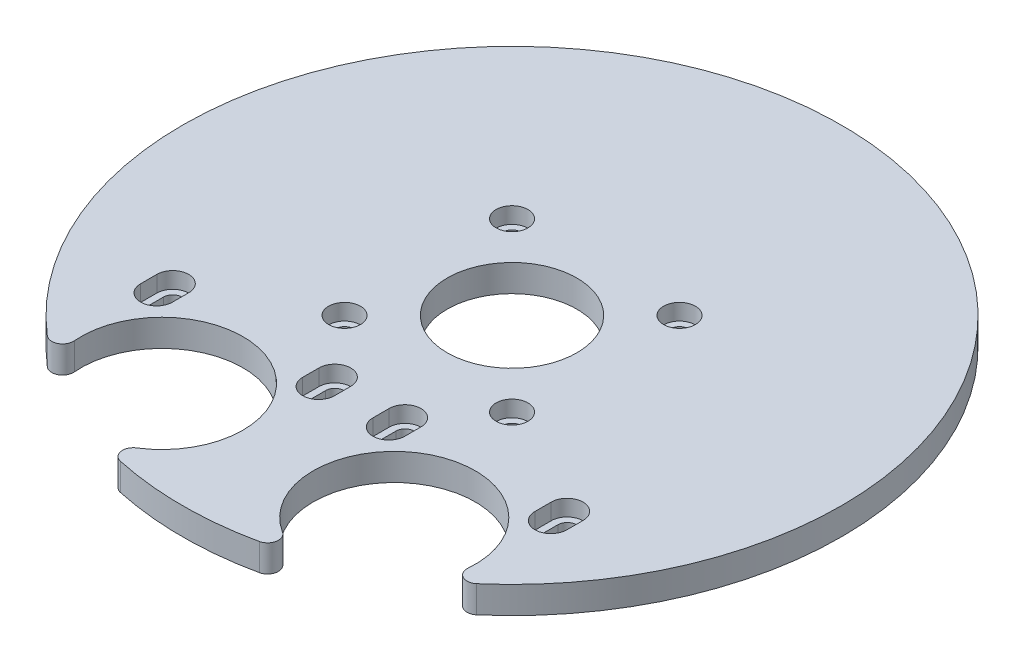
SolidWorks part; units mm, degrees
material "PLA"
ref_plane "Alzado" through (0, 0, 0) normal (0, 0, 1) x (1, 0, 0)
ref_plane "Planta" through (0, 0, 0) normal (0, 1, 0) x (1, 0, 0)
ref_plane "Vista lateral" through (0, 0, 0) normal (1, 0, 0) x (0, 0, -1)
sketch "Croquis1" plane through (0, 0, 0) normal (0, 1, 0) x (1, 0, 0)
  line L0 (0, 12) -> (0, -57.1022) construction
  arc A0 (-12.8483, -59.6315) -> (12.8483, -59.6315) centre (0, 0) ccw
  circle A1 centre (0, 0) radius 12
  arc A2 (-13.4944, -55.9851) -> (-36.4445, -44.5896) centre (-21.5, -43.3) ccw
  arc A4 (13.4944, -55.9851) -> (36.4445, -44.5896) centre (21.5, -43.3) cw
  arc A5 (39.74, -46.2788) -> (-39.74, -46.2788) centre (0, 0) ccw
  arc A6 (36.4445, -44.5896) -> (39.74, -46.2788) centre (38.4371, -44.7615) ccw
  arc A7 (13.4944, -55.9851) -> (12.8483, -59.6315) centre (12.427, -57.6764) cw
  arc A8 (-12.8483, -59.6315) -> (-13.4944, -55.9851) centre (-12.427, -57.6764) cw
  arc A9 (-39.74, -46.2788) -> (-36.4445, -44.5896) centre (-38.4371, -44.7615) ccw
  point P13 (34.9085, -50.0239)
  dimension "D3" = 30
  dimension "D4" = 24
  dimension "D5" = 122
  dimension "D6" = 2
  dimension "D1" = 21.5
  dimension "D2" = 43.3
extrude "Saliente-Extruir1" add sketch "Croquis1" along normal blind 5
sketch "Croquis2" plane through (0, 5, 0) normal (0, 1, 0) x (1, 0, 0)
  line L0 (-36.5, -26.3) -> (-36.5, -29.3) construction
  line L1 (15.5, -15.5) -> (-15.5, -15.5) construction
  line L2 (15.5, -15.5) -> (15.5, 15.5) construction
  line L3 (15.5, 15.5) -> (-15.5, 15.5) construction
  line L4 (-15.5, -15.5) -> (-15.5, 15.5) construction
  line L5 (15.5, -15.5) -> (-15.5, 15.5) construction
  line L6 (15.5, 15.5) -> (-15.5, -15.5) construction
  line L7 (-34.8, -26.3) -> (-34.8, -29.3)
  line L8 (-38.2, -26.3) -> (-38.2, -29.3)
  line L9 (-6.5, -26.3) -> (-6.5, -29.3) construction
  line L10 (-4.8, -26.3) -> (-4.8, -29.3)
  line L11 (-8.2, -26.3) -> (-8.2, -29.3)
  line L12 (0, 12) -> (0, -60.2233) construction
  line L13 (6.5, -26.3) -> (6.5, -29.3) construction
  line L14 (4.8, -26.3) -> (4.8, -29.3)
  line L15 (8.2, -26.3) -> (8.2, -29.3)
  line L16 (36.5, -26.3) -> (36.5, -29.3) construction
  line L17 (34.8, -26.3) -> (34.8, -29.3)
  line L18 (38.2, -26.3) -> (38.2, -29.3)
  circle A0 centre (-15.5, 15.5) radius 1.7
  circle A1 centre (-15.5, -15.5) radius 1.7
  circle A2 centre (15.5, -15.5) radius 1.7
  circle A3 centre (15.5, 15.5) radius 1.7
  arc A4 (-34.8, -26.3) -> (-38.2, -26.3) centre (-36.5, -26.3) ccw
  arc A5 (-38.2, -29.3) -> (-34.8, -29.3) centre (-36.5, -29.3) ccw
  arc A6 (-4.8, -26.3) -> (-8.2, -26.3) centre (-6.5, -26.3) ccw
  arc A7 (-8.2, -29.3) -> (-4.8, -29.3) centre (-6.5, -29.3) ccw
  arc A8 (-13.4944, -55.9851) -> (-36.4445, -44.5896) centre (-21.5, -43.3) ccw construction
  circle A9 centre (0, 0) radius 12 construction
  arc A10 (4.8, -26.3) -> (8.2, -26.3) centre (6.5, -26.3) cw
  arc A11 (8.2, -29.3) -> (4.8, -29.3) centre (6.5, -29.3) cw
  arc A12 (34.8, -26.3) -> (38.2, -26.3) centre (36.5, -26.3) cw
  arc A13 (38.2, -29.3) -> (34.8, -29.3) centre (36.5, -29.3) cw
  point P0 (0, 0)
  point P12 (-36.5, -27.8)
  point P17 (-6.5, -27.8)
  point P35 (6.5, -27.8)
  point P42 (36.5, -27.8)
  dimension "D2" = 3.4
  dimension "D5" = 15
  dimension "D7" = 1.7
  dimension "D1" = 31
  dimension "D3" = 14
  dimension "D4" = 15
  dimension "D6" = 3
extrude "Cortar-Extruir1" cut sketch "Croquis2" against normal blind 5
sketch "Croquis3" plane through (0, 5, 0) normal (0, 1, 0) x (1, 0, 0)
  line L0 (-36.5, -26.3) -> (-36.5, -29.3) construction
  line L1 (-33.55, -26.3) -> (-33.55, -29.3)
  line L2 (-39.45, -26.3) -> (-39.45, -29.3)
  line L3 (-6.5, -26.3) -> (-6.5, -29.3) construction
  line L4 (-3.55, -26.3) -> (-3.55, -29.3)
  line L5 (-9.45, -26.3) -> (-9.45, -29.3)
  line L6 (6.5, -26.3) -> (6.5, -29.3) construction
  line L7 (9.45, -26.3) -> (9.45, -29.3)
  line L8 (3.55, -26.3) -> (3.55, -29.3)
  line L9 (36.5, -26.3) -> (36.5, -29.3) construction
  line L10 (39.45, -26.3) -> (39.45, -29.3)
  line L11 (33.55, -26.3) -> (33.55, -29.3)
  circle A0 centre (-15.5, 15.5) radius 2.95
  circle A1 centre (15.5, 15.5) radius 2.95
  circle A2 centre (15.5, -15.5) radius 2.95
  circle A3 centre (-15.5, -15.5) radius 2.95
  arc A4 (-33.55, -26.3) -> (-39.45, -26.3) centre (-36.5, -26.3) ccw
  arc A5 (-39.45, -29.3) -> (-33.55, -29.3) centre (-36.5, -29.3) ccw
  arc A6 (-3.55, -26.3) -> (-9.45, -26.3) centre (-6.5, -26.3) ccw
  arc A7 (-9.45, -29.3) -> (-3.55, -29.3) centre (-6.5, -29.3) ccw
  arc A8 (9.45, -26.3) -> (3.55, -26.3) centre (6.5, -26.3) ccw
  arc A9 (3.55, -29.3) -> (9.45, -29.3) centre (6.5, -29.3) ccw
  arc A10 (39.45, -26.3) -> (33.55, -26.3) centre (36.5, -26.3) ccw
  arc A11 (33.55, -29.3) -> (39.45, -29.3) centre (36.5, -29.3) ccw
  point P16 (-36.5, -27.8)
  point P21 (-6.5, -27.8)
  point P30 (6.5, -27.8)
  point P39 (36.5, -27.8)
  dimension "D1" = 5.9
  dimension "D2" = 2.95
extrude "Cortar-Extruir2" cut sketch "Croquis3" against normal blind 3
